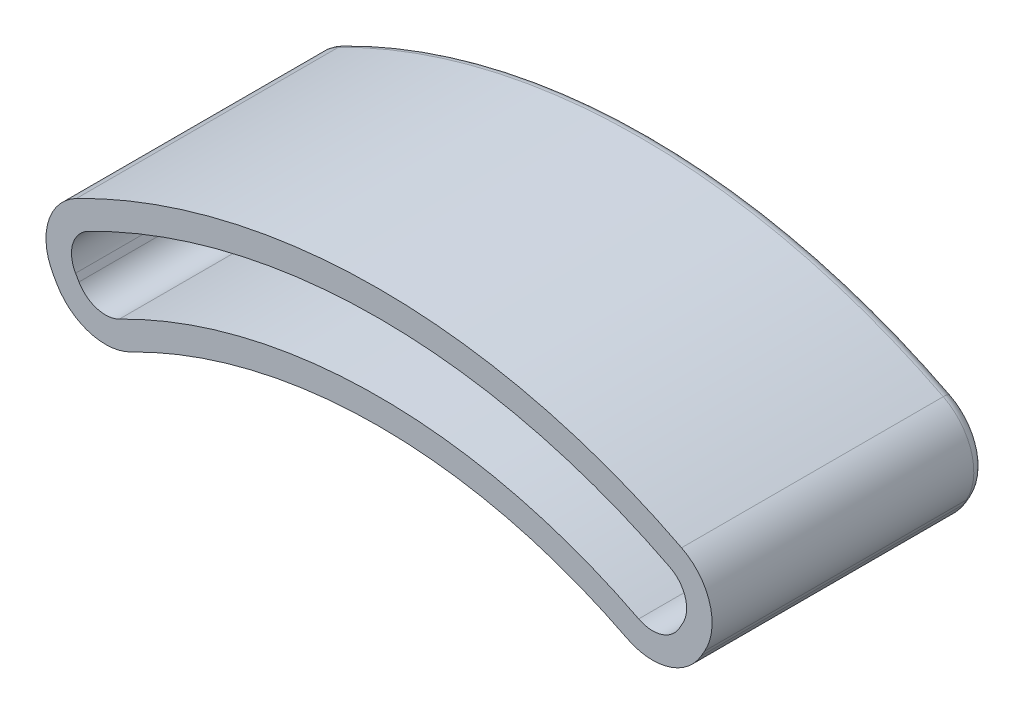
SolidWorks part; units mm, degrees
ref_plane "Front Plane" through (0, 0, 0) normal (0, 0, 1) x (1, 0, 0)
ref_plane "Top Plane" through (0, 0, 0) normal (0, 1, 0) x (1, 0, 0)
ref_plane "Right Plane" through (0, 0, 0) normal (1, 0, 0) x (0, 0, -1)
sketch "Sketch1" plane through (0, 0, 0) normal (0, 0, 1) x (1, 0, 0)
  line L0 (0, 0) -> (0, 42.62) construction
  line L1 (0, 0) -> (-21.31, 36.91) construction
  line L2 (0, 0) -> (21.31, 36.91) construction
  line L3 (-22.4239, 38.8393) -> (-22.6782, 39.2798)
  line L4 (22.4239, 38.8393) -> (22.6782, 39.2798)
  circle A0 centre (0, 0) radius 35 construction
  arc A1 (19.4034, 37.947) -> (-19.4034, 37.947) centre (0, 0) ccw
  arc A2 (21.7404, 42.4576) -> (-21.7404, 42.4576) centre (0, 0) ccw
  arc A3 (-22.4239, 38.8393) -> (-19.4034, 37.947) centre (-20.4442, 39.9823) ccw
  arc A4 (-22.6782, 39.2798) -> (-21.7404, 42.4576) centre (-20.6985, 40.4228) cw
  arc A5 (22.4239, 38.8393) -> (19.4034, 37.947) centre (20.4442, 39.9823) cw
  arc A6 (22.6782, 39.2798) -> (21.7404, 42.4576) centre (20.6985, 40.4228) ccw
  dimension "D1" = 70
  dimension "D2" = 7.62
  dimension "D5" = 5.08
  dimension "D6" = 2.286
  dimension "D3" = 30
  dimension "D4" = 30
extrude "Extrude-Thin2" add sketch "Sketch1" along normal blind 20.32 thin thin type one direction wall 1.905
fillet "Fillet2" radius 0.762 16 edges at (22.891, 41.0699, 0) (22.5511, 39.0596, 0) (21.0918, 37.79, 0) (0, 42.62, 0) (-21.0918, 37.79, 0) (-22.5511, 39.0596, 0) (-22.891, 41.0699, 0) (24.7181, 41.6091, 0) (24.2008, 38.1071, 0) (21.6316, 35.963, 0) (0, 40.715, 0) (-21.6316, 35.963, 0) (-24.2008, 38.1071, 0) (-24.7181, 41.6091, 0) (0, 47.7, 0) (0, 49.605, 0)
